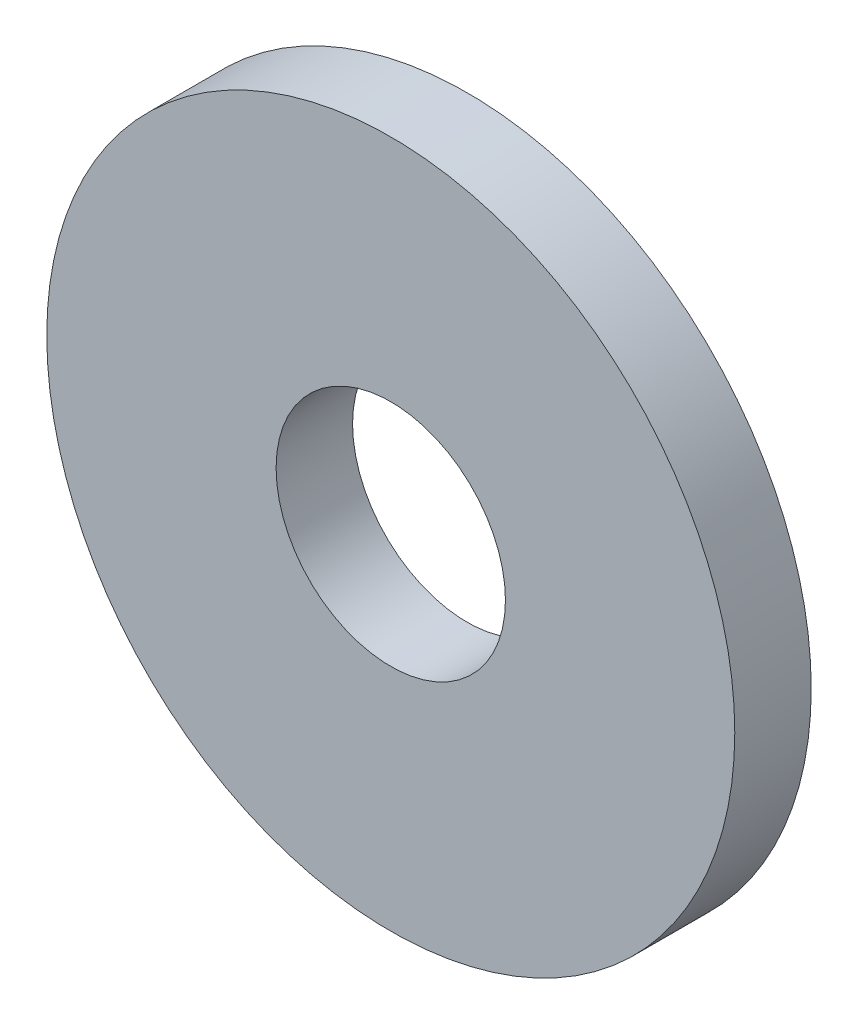
SolidWorks part; units mm, degrees
material "AISI 304"
ref_plane "前视基准面" through (0, 0, 0) normal (0, 0, 1) x (1, 0, 0)
ref_plane "上视基准面" through (0, 0, 0) normal (0, 1, 0) x (1, 0, 0)
ref_plane "右视基准面" through (0, 0, 0) normal (1, 0, 0) x (0, 0, -1)
sketch "草图1" plane through (0, 0, 0) normal (0, 0, 1) x (1, 0, 0)
  circle A0 centre (0, 0) radius 1.5
  circle A1 centre (0, 0) radius 4.5
  dimension "D1" = 3
  dimension "D2" = 9
extrude "凸台-拉伸1" add sketch "草图1" along normal blind 1
